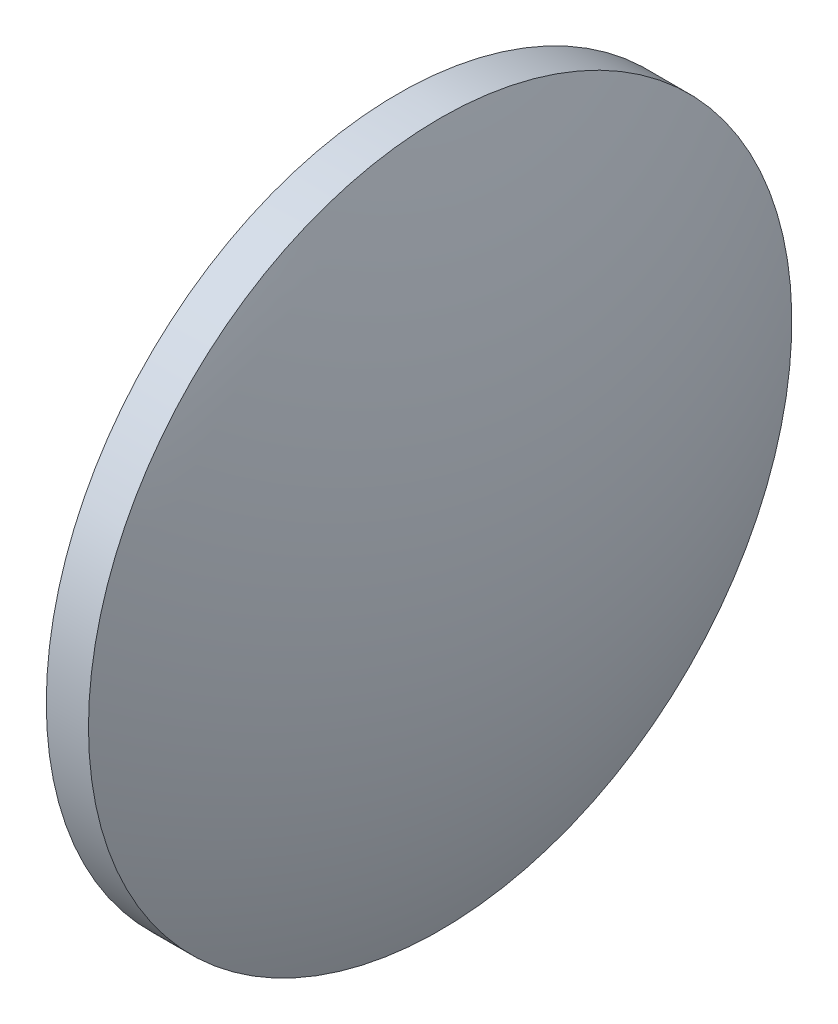
SolidWorks part; units mm, degrees
ref_plane "前视基准面" through (0, 0, 0) normal (0, 0, 1) x (1, 0, 0)
ref_plane "上视基准面" through (0, 0, 0) normal (0, 1, 0) x (1, 0, 0)
ref_plane "右视基准面" through (0, 0, 0) normal (1, 0, 0) x (0, 0, -1)
sketch "草图2" plane through (0, 0, 0) normal (0, 0, 1) x (1, 0, 0)
  line L0 (644.5807, 221.7118) -> (698.3637, 221.7118) construction
  line L1 (668.0489, 221.7118) -> (668.0489, 234.2118)
  line L2 (672.0489, 221.7118) -> (668.0489, 221.7118)
  line L5 (668.0489, 234.2118) -> (669.5489, 234.2118)
  arc A0 (672.0489, 221.7118) -> (669.5489, 234.2118) centre (639.5489, 221.7118) ccw
  dimension "D1" = 12.5
revolve "旋转2" add sketch "草图2" angle 360 about L0
